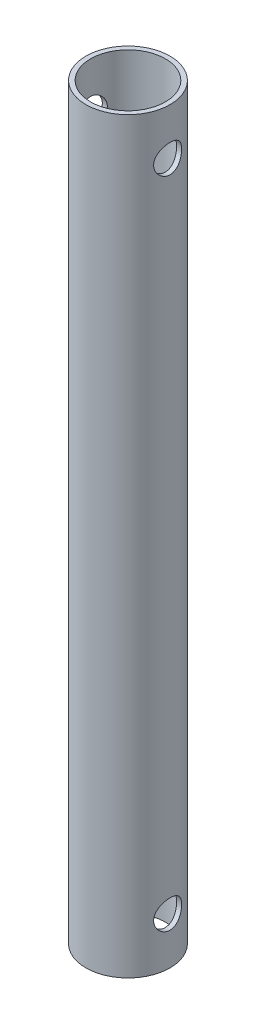
SolidWorks part; units mm, degrees
ref_plane "Alzado" through (0, 0, 0) normal (0, 0, 1) x (1, 0, 0)
ref_plane "Planta" through (0, 0, 0) normal (0, 1, 0) x (1, 0, 0)
ref_plane "Vista lateral" through (0, 0, 0) normal (1, 0, 0) x (0, 0, -1)
sketch "Croquis1" plane through (0, 0, 0) normal (0, 1, 0) x (1, 0, 0)
  circle A0 centre (0, 0) radius 4
  circle A1 centre (0, 0) radius 4.5
  dimension "D1" = 9
  dimension "D2" = 8
extrude "Saliente-Extruir1" add sketch "Croquis1" along normal blind 80
sketch "Croquis2" plane through (0, 0, 0) normal (1, 0, 0) x (0, 0, -1)
  line L0 (0, 0) -> (0, 5) construction
  line L1 (0, 5) -> (0, 75) construction
  line L2 (0, 75) -> (0, 80) construction
  line L3 (4.5, 80) -> (-4.5, 80) construction
  circle A0 centre (0, 75) radius 1.5
  circle A1 centre (0, 5) radius 1.5
  dimension "D3" = 3
  dimension "D1" = 5
  dimension "D2" = 5
extrude "Cortar-Extruir1" cut sketch "Croquis2" against normal through all and the other way through all
